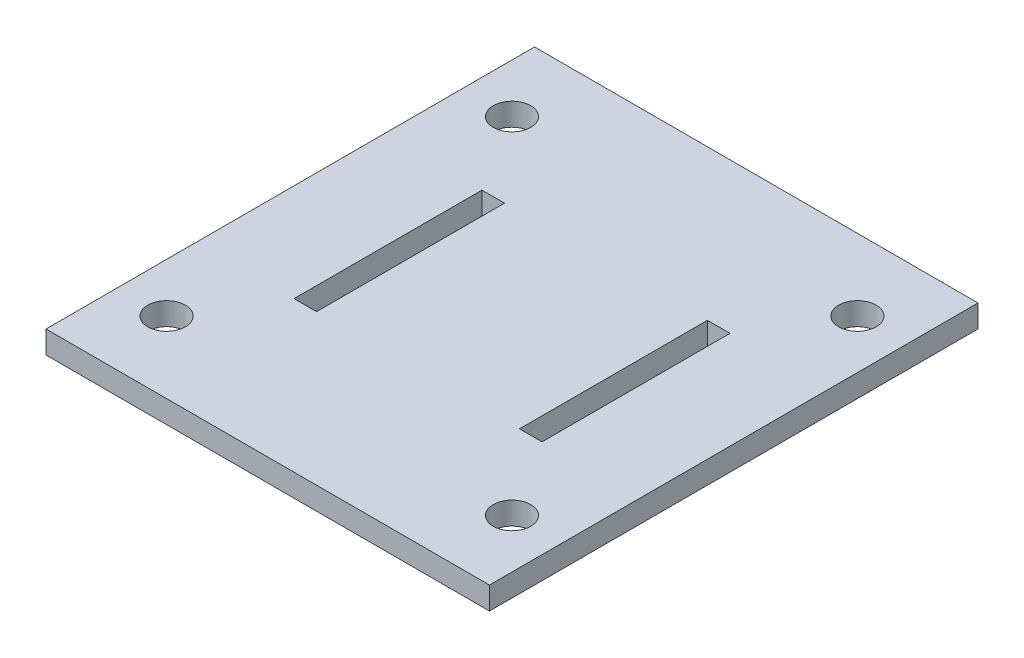
SolidWorks part; units mm, degrees
ref_plane "Front Plane" through (0, 0, 0) normal (0, 0, 1) x (1, 0, 0)
ref_plane "Top Plane" through (0, 0, 0) normal (0, 1, 0) x (1, 0, 0)
ref_plane "Right Plane" through (0, 0, 0) normal (1, 0, 0) x (0, 0, -1)
sketch "Sketch1" plane through (0, 0, 0) normal (0, 1, 0) x (1, 0, 0)
  line L0 (-29.5, 12.5) -> (-29.5, -12.5)
  line L1 (-32.5, -32.5) -> (32.5, -32.5)
  line L2 (-32.5, -32.5) -> (-32.5, 32.5)
  line L3 (-32.5, 32.5) -> (32.5, 32.5)
  line L4 (32.5, -32.5) -> (32.5, 32.5)
  line L5 (-32.5, -32.5) -> (32.5, 32.5) construction
  line L6 (-32.5, 32.5) -> (32.5, -32.5) construction
  line L15 (-32.5, 32.5) -> (-29.5, 32.5)
  line L16 (-32.5, 32.5) -> (-32.5, 12.5)
  line L17 (-32.5, 12.5) -> (-29.5, 12.5)
  line L18 (-29.5, 32.5) -> (-29.5, 12.5)
  line L19 (-32.5, -32.5) -> (-29.5, -32.5)
  line L20 (-32.5, -32.5) -> (-32.5, -12.5)
  line L21 (-32.5, -12.5) -> (-29.5, -12.5)
  line L22 (-29.5, -32.5) -> (-29.5, -12.5)
  line L23 (32.5, 32.5) -> (29.5, 32.5)
  line L24 (32.5, 32.5) -> (32.5, 12.5)
  line L25 (32.5, 12.5) -> (29.5, 12.5)
  line L26 (29.5, 32.5) -> (29.5, 12.5)
  line L27 (32.5, -32.5) -> (29.5, -32.5)
  line L28 (32.5, -32.5) -> (32.5, -12.5)
  line L29 (32.5, -12.5) -> (29.5, -12.5)
  line L30 (29.5, -32.5) -> (29.5, -12.5)
  line L31 (13.5, -12.5) -> (16.5, -12.5)
  line L32 (13.5, -12.5) -> (13.5, 12.5)
  line L33 (13.5, 12.5) -> (16.5, 12.5)
  line L34 (16.5, -12.5) -> (16.5, 12.5)
  line L35 (13.5, -12.5) -> (16.5, 12.5) construction
  line L36 (13.5, 12.5) -> (16.5, -12.5) construction
  line L37 (-16.5, -12.5) -> (-13.5, -12.5)
  line L38 (-16.5, -12.5) -> (-16.5, 12.5)
  line L39 (-16.5, 12.5) -> (-13.5, 12.5)
  line L40 (-13.5, -12.5) -> (-13.5, 12.5)
  line L41 (-16.5, -12.5) -> (-13.5, 12.5) construction
  line L42 (-16.5, 12.5) -> (-13.5, -12.5) construction
  line L43 (29.5, -12.5) -> (29.5, 12.5)
  line L44 (29.5, 12.5) -> (29.5, -12.5)
  circle A0 centre (22.981, -22.981) radius 2.5
  circle A1 centre (-22.981, -22.981) radius 2.5
  circle A2 centre (-22.981, 22.981) radius 2.5
  circle A3 centre (22.981, 22.981) radius 2.5
  point P0 (0, 0)
  point P15 (15, 0)
  point P31 (0, 0)
  point P32 (-15, 0)
  dimension "D7" = 5
  dimension "D1" = 65
  dimension "D2" = 65
  dimension "D3" = 3
  dimension "D4" = 20
  dimension "D5" = 20
  dimension "D6" = 3
  dimension "D8" = 32.5
  dimension "D9" = 3
  dimension "D10" = 20
  dimension "D11" = 20
  dimension "D12" = 3
  dimension "D14" = 25
  dimension "D15" = 25
  dimension "D16" = 3
  dimension "D17" = 3
  dimension "D18" = 15
  dimension "D19" = 15
  dimension "D13" = 4
extrude "Boss-Extrude1" add sketch "Sketch1" along normal blind 3
